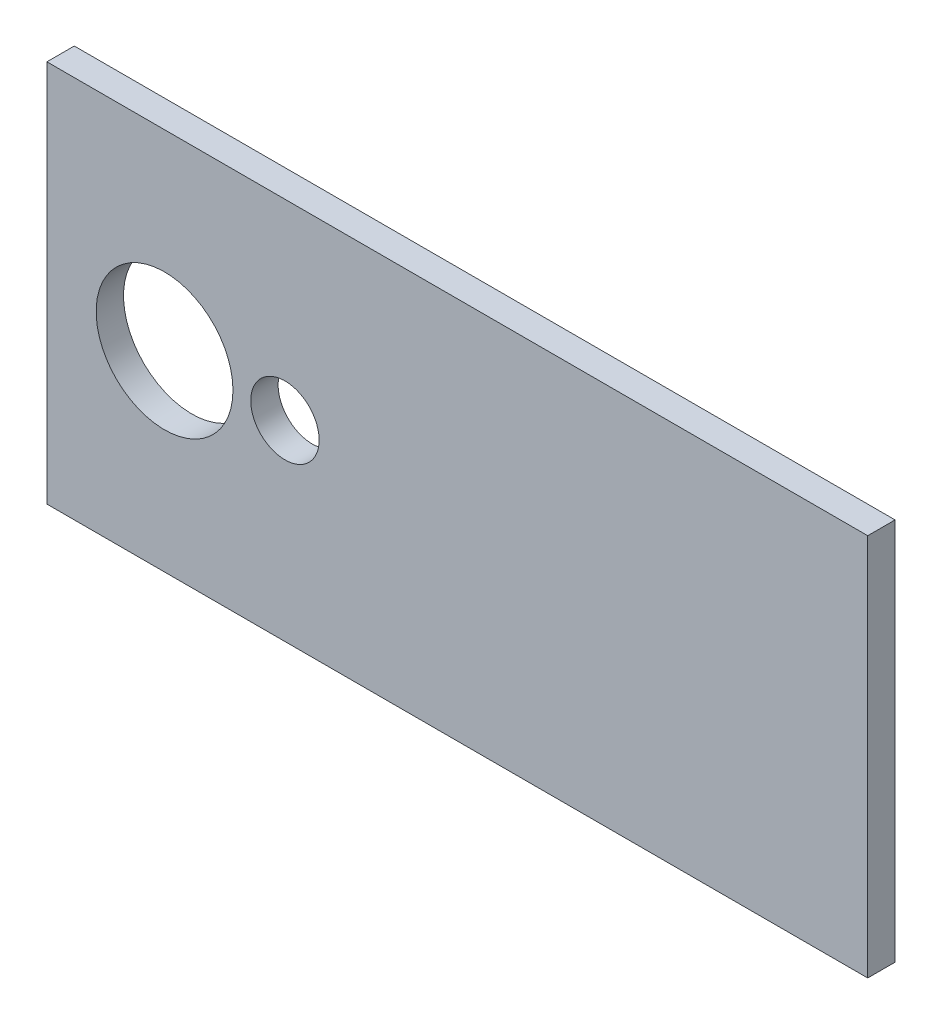
SolidWorks part; units mm, degrees
material "Maple"
ref_plane "Front Plane" through (0, 0, 0) normal (0, 0, 1) x (1, 0, 0)
ref_plane "Top Plane" through (0, 0, 0) normal (0, 1, 0) x (1, 0, 0)
ref_plane "Right Plane" through (0, 0, 0) normal (1, 0, 0) x (0, 0, -1)
sketch "Sketch1" plane through (0, 0, 0) normal (0, 0, 1) x (1, 0, 0)
  line L1 (-95.25, 44.45) -> (95.25, 44.45)
  line L2 (-95.25, 44.45) -> (-95.25, -44.45)
  line L3 (-95.25, -44.45) -> (95.25, -44.45)
  line L4 (95.25, 44.45) -> (95.25, -44.45)
  line L5 (-95.25, 44.45) -> (95.25, -44.45) construction
  line L6 (-95.25, -44.45) -> (95.25, 44.45) construction
  circle A0 centre (-67.945, 0) radius 15.875
  circle A1 centre (-40.005, 0) radius 7.9375
  point P0 (0, 0)
  dimension "D3" = 31.75
  dimension "D4" = 15.875
  dimension "D1" = 88.9
  dimension "D2" = 190.5
  dimension "D5" = 27.94
  dimension "D6" = 27.305
extrude "Boss-Extrude1" add sketch "Sketch1" along normal mid plane 6.35
